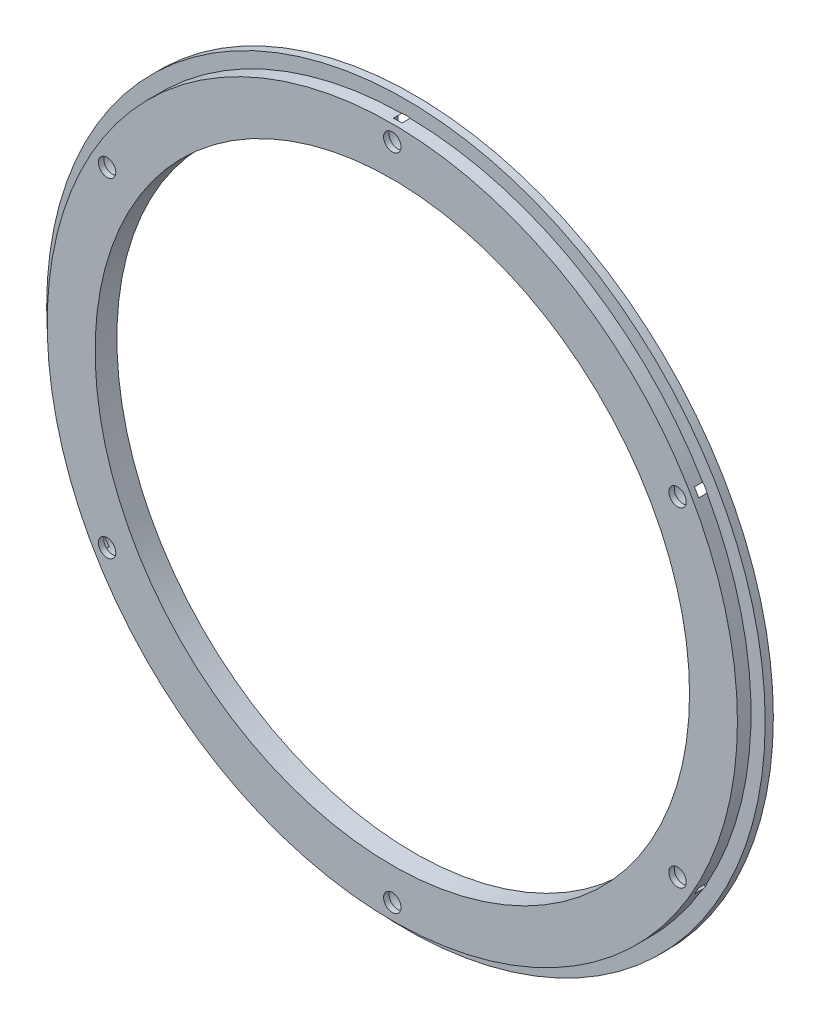
SolidWorks part; units mm, degrees
ref_plane "Front Plane" through (0, 0, 0) normal (0, 0, 1) x (1, 0, 0)
ref_plane "Top Plane" through (0, 0, 0) normal (0, 1, 0) x (1, 0, 0)
ref_plane "Right Plane" through (0, 0, 0) normal (1, 0, 0) x (0, 0, -1)
sketch "Sketch1" plane through (0, 0, 0) normal (0, 0, 1) x (1, 0, 0)
  circle A0 centre (0, 0) radius 66
extrude "Boss-Extrude1" add sketch "Sketch1" along normal blind 1.5
sketch "Sketch2" plane through (0, 0, 1.5) normal (0, 0, 1) x (1, 0, 0)
  circle A0 centre (0, 0) radius 63.4
extrude "Boss-Extrude2" add sketch "Sketch2" along normal blind 2.5
sketch "Sketch3" plane through (0, 0, 4) normal (0, 0, 1) x (1, 0, 0)
  circle A0 centre (0, 0) radius 54.6
extrude "Cut-Extrude1" cut sketch "Sketch3" against normal blind 10
sketch "Sketch4" plane through (0, 0, 4) normal (0, 0, 1) x (1, 0, 0)
  circle A1 centre (0, 60.5) radius 1.6
  circle A2 centre (52.3945, 30.25) radius 1.6
  circle A3 centre (52.3945, -30.25) radius 1.6
  circle A4 centre (0, -60.5) radius 1.6
  circle A5 centre (-52.3945, -30.25) radius 1.6
  circle A6 centre (-52.3945, 30.25) radius 1.6
  point P16 (0, 0)
  dimension "D1" = 6
extrude "Cut-Extrude2" cut sketch "Sketch4" against normal blind 10
sketch "Sketch5" plane through (0, 0, 0) normal (0, 0, -1) x (-1, 0, 0)
  circle A0 centre (-52.3945, 30.25) radius 3
  circle A1 centre (0, 60.5) radius 3
  circle A2 centre (-52.3945, -30.25) radius 3
  circle A3 centre (0, -60.5) radius 3
  circle A4 centre (52.3945, -30.25) radius 3
  circle A5 centre (52.3945, 30.25) radius 3
extrude "Cut-Extrude3" cut sketch "Sketch5" against normal blind 3
